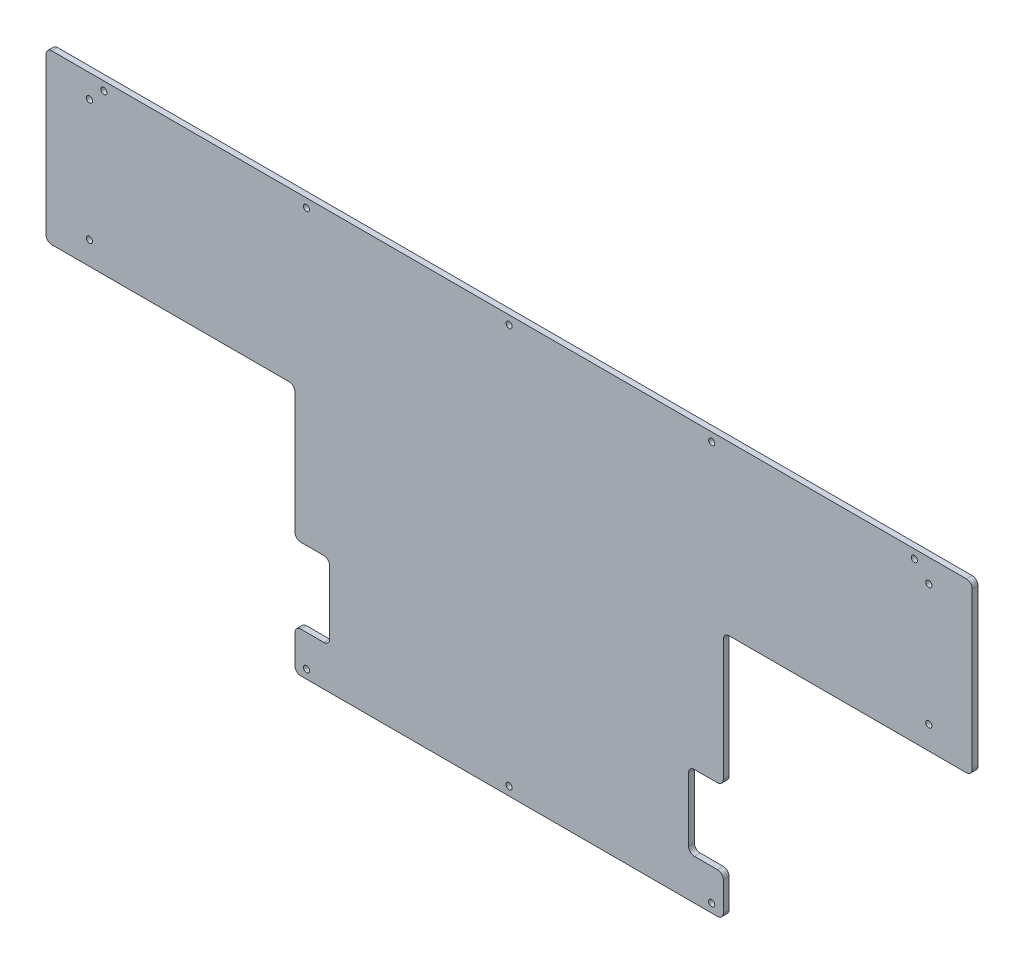
SolidWorks part; units mm, degrees
material "PC High Viscosity"
ref_plane "Front Plane" through (0, 0, 0) normal (0, 0, 1) x (1, 0, 0)
ref_plane "Top Plane" through (0, 0, 0) normal (0, 1, 0) x (1, 0, 0)
ref_plane "Right Plane" through (0, 0, 0) normal (1, 0, 0) x (0, 0, -1)
sketch "Sketch1" plane through (0, 0, 0) normal (0, 0, 1) x (1, 0, 0)
  line L0 (-508, 0) -> (508, 0)
  line L1 (508, 0) -> (508, -184.15)
  line L2 (508, -184.15) -> (234.95, -184.15)
  line L3 (234.95, -184.15) -> (234.95, -457.2)
  line L4 (234.95, -457.2) -> (-234.95, -457.2)
  line L5 (-234.95, -457.2) -> (-234.95, -184.15)
  line L6 (-234.95, -184.15) -> (-508, -184.15)
  line L7 (-508, -184.15) -> (-508, 0)
  point P9 (0, 0)
  dimension "D1" = 457.2
  dimension "D2" = 273.05
  dimension "D3" = 273.05
  dimension "D4" = 1016
extrude "Boss-Extrude1" add sketch "Sketch1" along normal blind 6.35
sketch "Sketch2" plane through (0, 0, 6.35) normal (0, 0, 1) x (1, 0, 0)
  line L0 (508, 0) -> (-508, 0) construction
  line L1 (-234.95, -457.2) -> (234.95, -457.2) construction
  circle A0 centre (0, -9.525) radius 3.3655
  circle A1 centre (0, -447.675) radius 3.3655
  circle A2 centre (222.25, -9.525) radius 3.3655
  circle A3 centre (222.25, -447.675) radius 3.3655
  circle A4 centre (444.5, -9.525) radius 3.3655
  circle A6 centre (444.5, -447.675) radius 3.3655 [skipped]
  circle A7 centre (-222.25, -9.525) radius 3.3655
  circle A8 centre (-222.25, -447.675) radius 3.3655
  circle A9 centre (-444.5, -9.525) radius 3.3655
  circle A11 centre (-444.5, -447.675) radius 3.3655 [skipped]
  dimension "D1" = 9.525
  dimension "D3" = 6.731
  dimension "D2" = 9.525
  dimension "D6" = 222.25
  dimension "D7" = 222.25
  dimension "D4" = 3
  dimension "D5" = 3
extrude "Cut-Extrude1" cut sketch "Sketch2" against normal through all
sketch "Sketch3" plane through (0, 0, 6.35) normal (0, 0, 1) x (1, 0, 0)
  line L0 (-508, 0) -> (-508, -184.15) construction
  line L1 (508, 0) -> (-508, 0) construction
  line L2 (-508, -184.15) -> (-234.95, -184.15) construction
  circle A0 centre (-460.375, -25.4) radius 3.3655
  circle A1 centre (-460.375, -158.75) radius 3.3655
  dimension "D1" = 47.625
  dimension "D2" = 6.731
  dimension "D3" = 25.4
  dimension "D4" = 25.4
extrude "Cut-Extrude2" cut sketch "Sketch3" against normal through all
mirror "Mirror1" about plane through (0, 0, 0) normal (1, 0, 0) of "Cut-Extrude2"
sketch "Sketch5" plane through (0, 0, 6.35) normal (0, 0, 1) x (1, 0, 0)
  line L0 (-234.95, -330.2) -> (-196.85, -330.2)
  line L1 (-234.95, -330.2) -> (-234.95, -412.75)
  line L2 (-196.85, -330.2) -> (-196.85, -412.75)
  line L3 (-234.95, -412.75) -> (-196.85, -412.75)
  line L4 (-234.95, -184.15) -> (-234.95, -457.2) construction
  line L5 (-234.95, -457.2) -> (234.95, -457.2) construction
  dimension "D1" = 44.45
  dimension "D2" = 82.55
  dimension "D3" = 38.1
extrude "Cut-Extrude3" cut sketch "Sketch5" against normal through all
mirror "Mirror2" about plane through (0, 0, 0) normal (1, 0, 0) of "Cut-Extrude3"
fillet "Fillet1" radius 6.35 16 edges at (-234.95, -412.75, 3.175) (-196.85, -412.75, 3.175) (-196.85, -330.2, 3.175) (-234.95, -330.2, 3.175) (-508, -184.15, 3.175) (-508, 0, 3.175) (508, 0, 3.175) (508, -184.15, 3.175) (234.95, -184.15, 3.175) (234.95, -457.2, 3.175) (-234.95, -457.2, 3.175) (-234.95, -184.15, 3.175) (234.95, -330.2, 3.175) (234.95, -412.75, 3.175) (196.85, -412.75, 3.175) (196.85, -330.2, 3.175)
